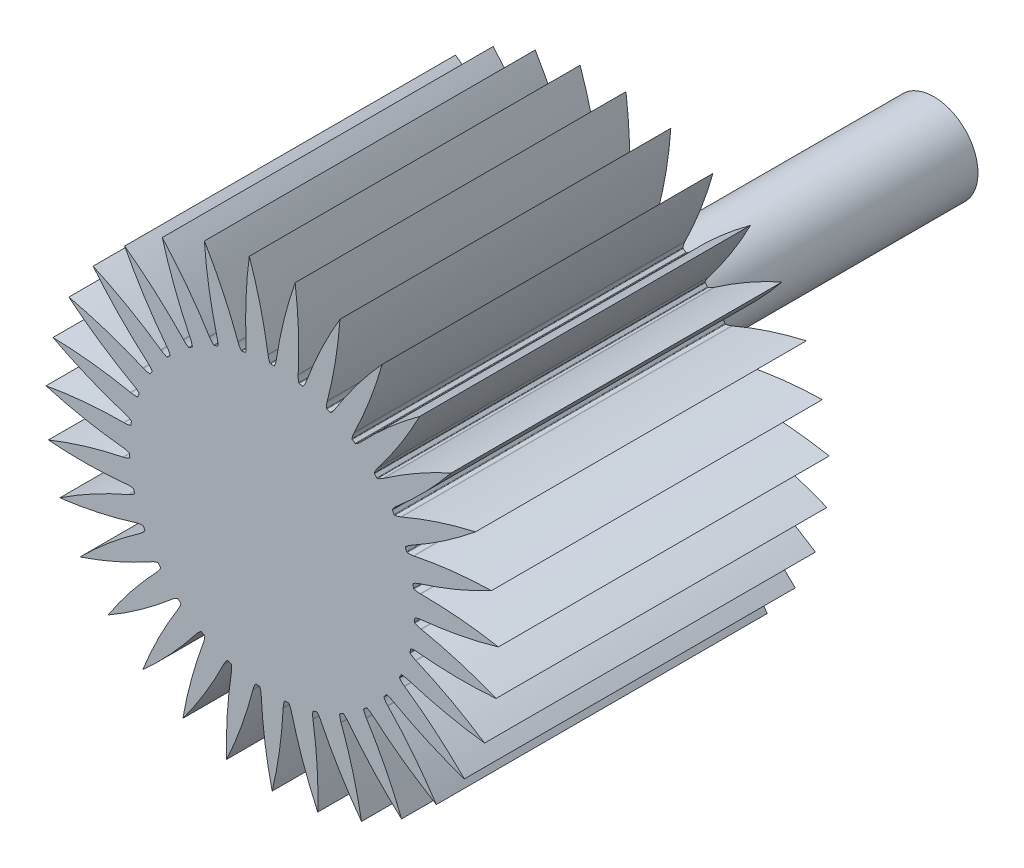
SolidWorks part; units mm, degrees
material "Pure Gold"
ref_plane "Front" through (0, 0, 0) normal (0, 0, 1) x (1, 0, 0)
ref_plane "Top" through (0, 0, 0) normal (0, 1, 0) x (1, 0, 0)
ref_plane "Right" through (0, 0, 0) normal (1, 0, 0) x (0, 0, -1)
sketch "Sketch1" plane through (0, 0, 0) normal (0, 0, 1) x (1, 0, 0)
  line L0 (0, 0) -> (0, 500) construction
  circle A1 centre (0, 0) radius 500
  dimension "D1" = 1000
extrude "Extrude1" add sketch "Sketch1" along normal blind 300
sketch "Sketch2" plane through (0, 0, 300) normal (0, 0, 1) x (1, 0, 0)
  line L0 (0, 0) -> (0, 500) construction
  line L1 (3.7322, 135.1942) -> (3.81, 135.7022)
  line L2 (-3.7322, 135.1942) -> (-3.81, 135.7022)
  circle A0 centre (0, 0) radius 500 construction
  arc A1 (1.905, 129.3522) -> (-1.905, 129.3522) centre (0, 0) ccw
  arc A2 (1.905, 129.3522) -> (3.7322, 135.1942) centre (-16.3537, 138.2697) ccw
  arc A3 (3.81, 135.7022) -> (241.2315, 437.9582) centre (390.2485, 76.5306) cw
  arc A4 (-3.81, 135.7022) -> (-241.2315, 437.9582) centre (-390.2485, 76.5306) ccw
  arc A5 (-1.905, 129.3522) -> (-3.7322, 135.1942) centre (16.3537, 138.2697) cw
  dimension "D1" = 7.62
  dimension "D2" = 20.32
  dimension "D4" = 6.35
  dimension "D5" = 3.81
  dimension "D6" = 129.3662
  dimension "D7" = 390.9425
  dimension "D3" = 0.508
extrude "Cut-Extrude1" cut sketch "Sketch2" against normal through all and the other way through all flip side to cut
fillet "Fillet1" radius 0.635 2 edges at (1.905, 129.3522, 150) (-1.905, 129.3522, 150)
pattern_circular "CirPattern1" count 31 over 360 about axis through (0, 0, 0) along (0, 0, 1) of "Cut-Extrude1", "Fillet1"
sketch "Sketch3" plane through (0, 0, 0) normal (0, 0, -1) x (-1, 0, 0)
  circle A0 centre (0, 0) radius 40
  dimension "D1" = 80
extrude "Extrude2" add sketch "Sketch3" along normal blind 300
equation "\"wheelSize\"= 100cm"
equation "\"D1@Sketch1\"=\"wheelSize\""
equation "\"D1@Sketch3\" = \"HoleMountDiameter@PrintingPress.Assembly\""
equation "\"D1@Extrude2\" = 3 * \"RivetLength@PrintingPress.Assembly\""
equation "\"wheelThickness\"= 3 * \"RivetLength@PrintingPress.Assembly\""
equation "\"D1@Extrude1\"=\"wheelThickness\""
